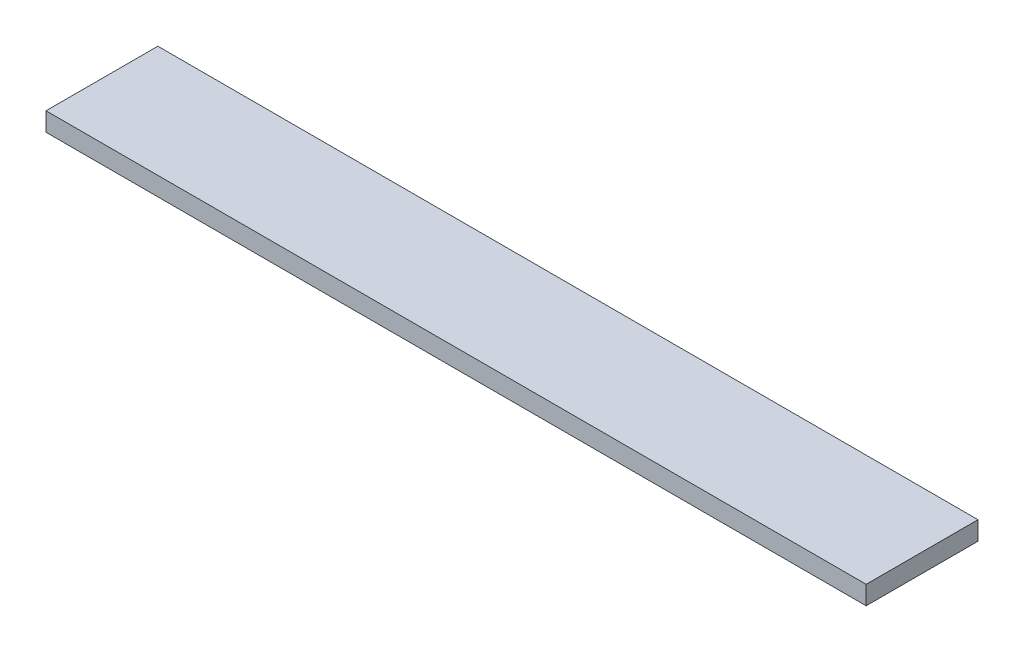
SolidWorks part; units mm, degrees
ref_plane "Front Plane" through (0, 0, 0) normal (0, 0, 1) x (1, 0, 0)
ref_plane "Top Plane" through (0, 0, 0) normal (0, 1, 0) x (1, 0, 0)
ref_plane "Right Plane" through (0, 0, 0) normal (1, 0, 0) x (0, 0, -1)
sketch "Sketch1" plane through (0, 0, 0) normal (0, 1, 0) x (1, 0, 0)
  line L1 (0, 0) -> (139.7, 0)
  line L2 (0, 0) -> (0, -19.05)
  line L3 (0, -19.05) -> (139.7, -19.05)
  line L4 (139.7, 0) -> (139.7, -19.05)
  dimension "D1" = 19.05
  dimension "D2" = 139.7
extrude "Boss-Extrude1" add sketch "Sketch1" along normal blind 3.175
